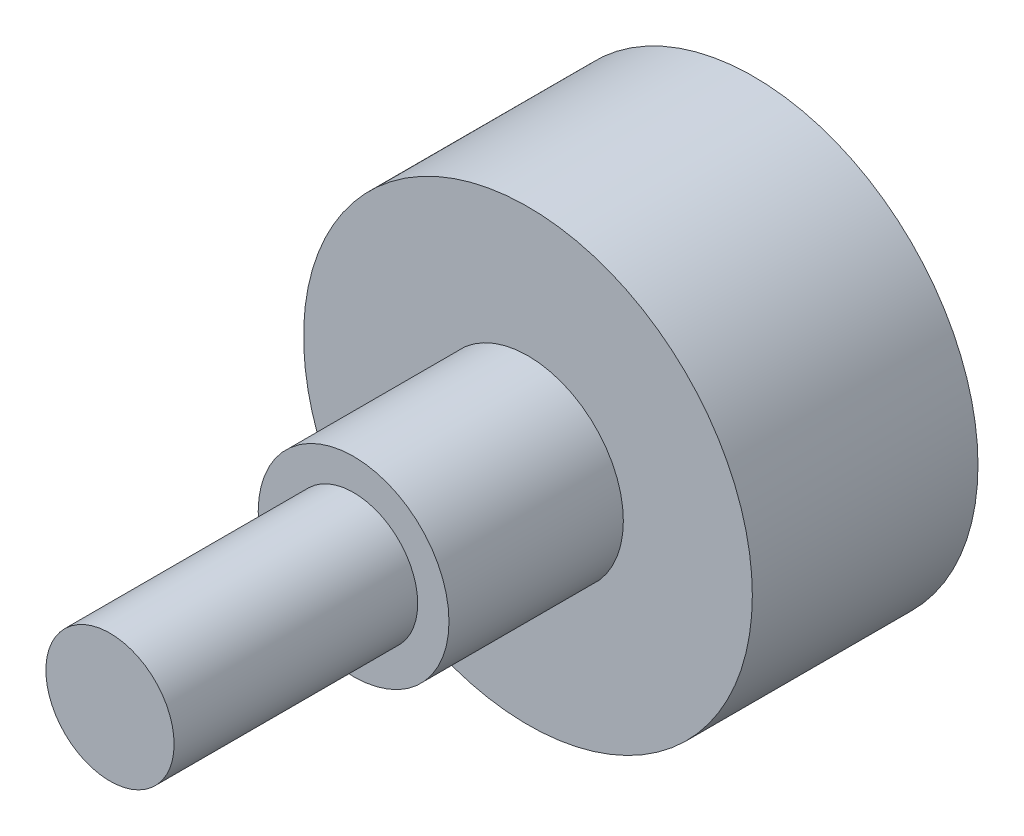
SolidWorks part; units mm, degrees
ref_plane "Front Plane" through (0, 0, 0) normal (0, 0, 1) x (1, 0, 0)
ref_plane "Top Plane" through (0, 0, 0) normal (0, 1, 0) x (1, 0, 0)
ref_plane "Right Plane" through (0, 0, 0) normal (1, 0, 0) x (0, 0, -1)
sketch "Sketch1" plane through (0, 0, 0) normal (0, 0, 1) x (1, 0, 0)
  circle A0 centre (0, 0) radius 11.1125
  dimension "D1" = 22.225
extrude "Boss-Extrude1" add sketch "Sketch1" along normal blind 11.176
sketch "Sketch2" plane through (0, 0, 11.176) normal (0, 0, 1) x (1, 0, 0)
  circle A0 centre (0, 0) radius 4.7244
  dimension "D1" = 9.4488
extrude "Boss-Extrude2" add sketch "Sketch2" along normal blind 8.636
sketch "Sketch3" plane through (0, 0, 19.812) normal (0, 0, 1) x (1, 0, 0)
  circle A0 centre (0, 0) radius 3.175
  dimension "D1" = 6.35
extrude "Boss-Extrude3" add sketch "Sketch3" along normal blind 12.065
